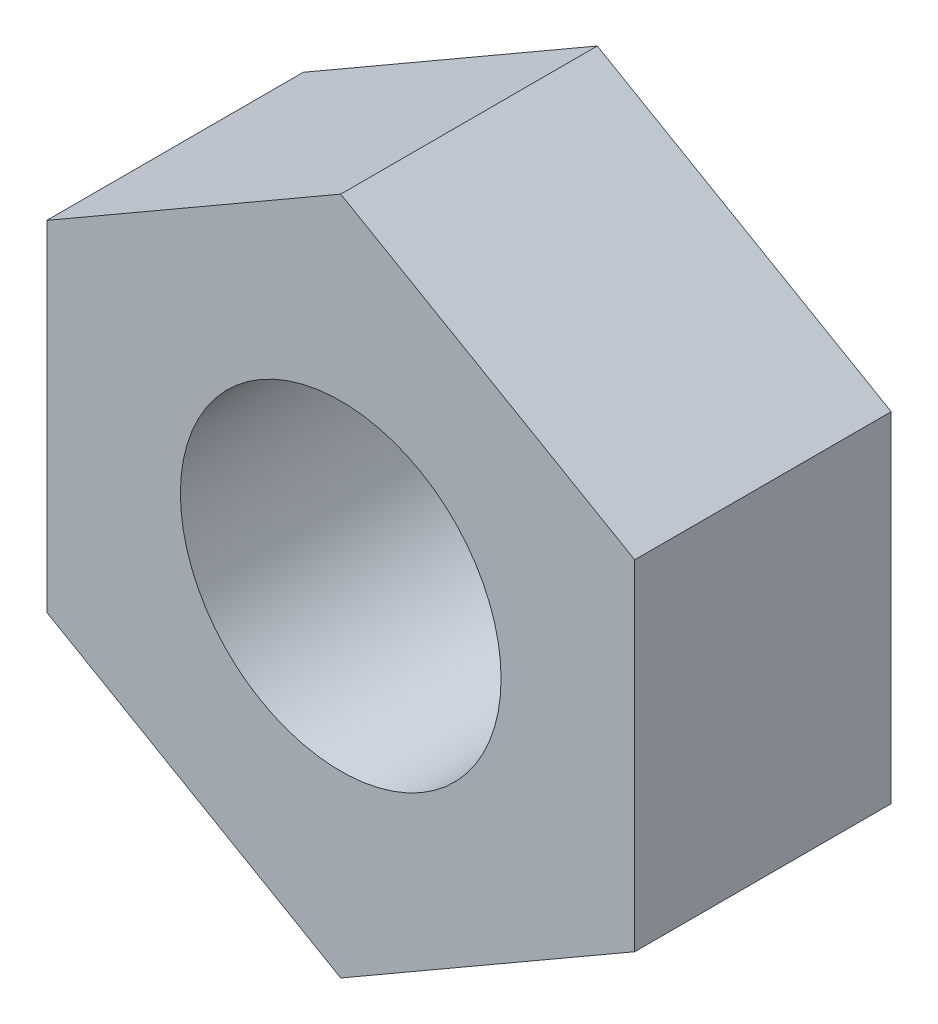
SolidWorks part; units mm, degrees
ref_plane "Plan de face" through (0, 0, 0) normal (0, 0, 1) x (1, 0, 0)
ref_plane "Plan de dessus" through (0, 0, 0) normal (0, 1, 0) x (1, 0, 0)
ref_plane "Plan de droite" through (0, 0, 0) normal (1, 0, 0) x (0, 0, -1)
sketch "Esquisse1" plane through (0, 0, 0) normal (0, 0, 1) x (1, 0, 0)
  line L1 (0, -3.1754) -> (2.75, -1.5877)
  line L2 (2.75, -1.5877) -> (2.75, 1.5877)
  line L3 (2.75, 1.5877) -> (0, 3.1754)
  line L4 (0, 3.1754) -> (-2.75, 1.5877)
  line L5 (-2.75, 1.5877) -> (-2.75, -1.5877)
  line L6 (-2.75, -1.5877) -> (0, -3.1754)
  circle A0 centre (0, 0) radius 2.75 construction
  circle A1 centre (0, 0) radius 1.5
  dimension "D2" = 3
  dimension "D1" = 5.5
extrude "Boss.-Extru.1" add sketch "Esquisse1" along normal blind 2.4
